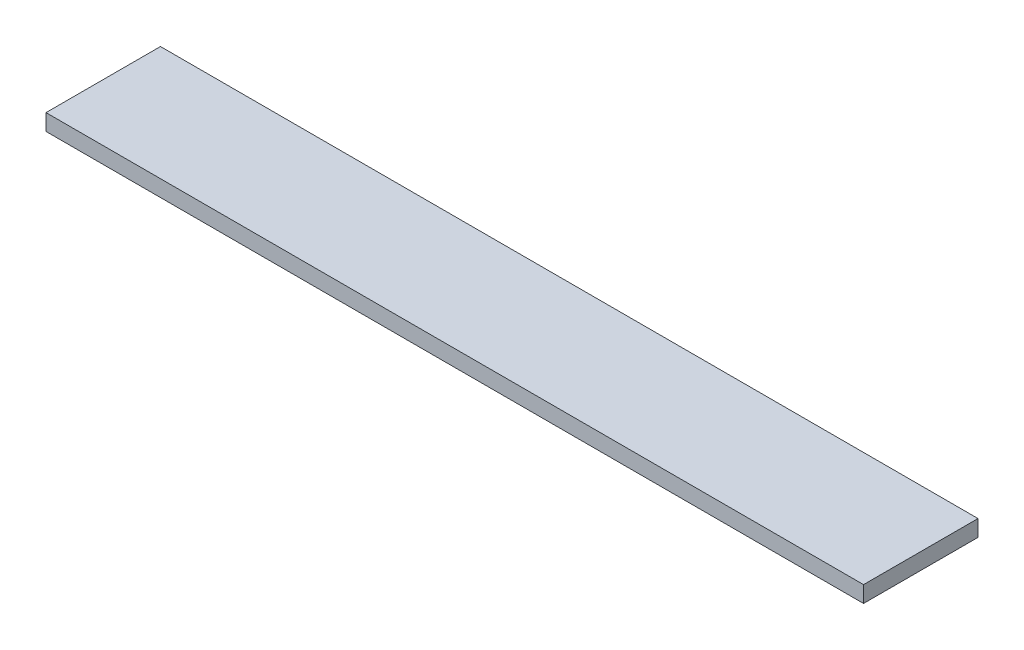
SolidWorks part; units mm, degrees
ref_plane "Front Plane" through (0, 0, 0) normal (0, 0, 1) x (1, 0, 0)
ref_plane "Top Plane" through (0, 0, 0) normal (0, 1, 0) x (1, 0, 0)
ref_plane "Right Plane" through (0, 0, 0) normal (1, 0, 0) x (0, 0, -1)
sketch "Sketch1" plane through (0, 0, 0) normal (0, 1, 0) x (1, 0, 0)
  line L1 (-250, -35) -> (250, -35)
  line L2 (-250, -35) -> (-250, 35)
  line L3 (-250, 35) -> (250, 35)
  line L4 (250, -35) -> (250, 35)
  line L5 (-250, -35) -> (250, 35) construction
  line L6 (-250, 35) -> (250, -35) construction
  point P0 (0, 0)
  dimension "D1" = 500
  dimension "D2" = 70
extrude "Boss-Extrude1" add sketch "Sketch1" along normal blind 10
